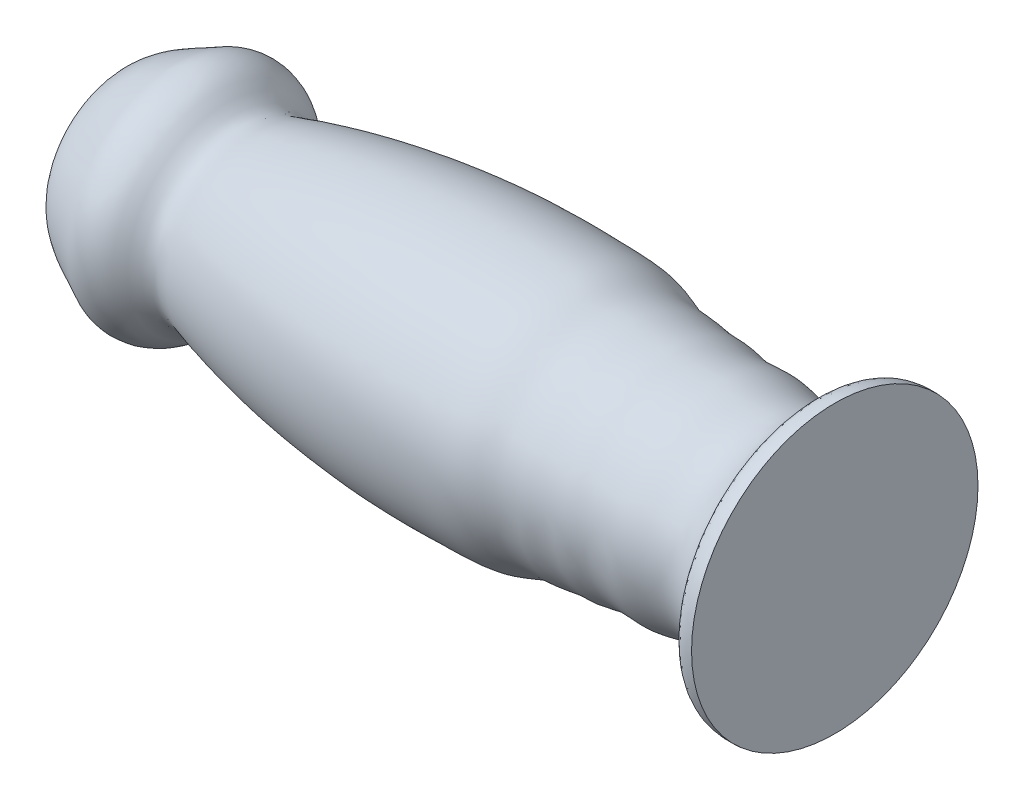
SolidWorks part; units mm, degrees
ref_plane "Front Plane" through (0, 0, 0) normal (0, 0, 1) x (1, 0, 0)
ref_plane "Top Plane" through (0, 0, 0) normal (0, 1, 0) x (1, 0, 0)
ref_plane "Right Plane" through (0, 0, 0) normal (1, 0, 0) x (0, 0, -1)
sketch "Sketch2" plane through (0, 0, 0) normal (0, 1, 0) x (1, 0, 0)
  line L0 (0, 0) -> (76.2, 0) construction
  line L1 (0, -12.7) -> (0, 12.7) construction
  line L2 (41.9716, 155.783) -> (-4.8564, -161.233) construction
  line L3 (-48.8594, 0.7428) -> (21.0217, -260.0572) construction
  line L4 (76.2, 15.2345) -> (76.2, 0)
  line L5 (76.2, 0) -> (0, 0)
  spline S0 degree 3 poles (0, 0) (-0.0143, 1.4775) (0.166, 4.2425) (-0.326, 7.6135) (2.2489, 9.9053) (4.7524, 10.8813) (7.3314, 12.3666) (10.5485, 11.8001) (12.4487, 8.7803) (14.9296, 9.7162) (17.742, 10.4735) (23.0715, 11.7188) (28.7793, 12.5633) (35.419, 13.1824) (40.362, 13.3) (45.5684, 13.1787) (49.2634, 13.0947) (52.1358, 11.6382) (54.6249, 11.7097) (56.5581, 11.2463) (58.6813, 11.3604) (60.9893, 10.6348) (64.4642, 11.339) (69.2158, 9.2572) (73.3406, 12.1818) (74.5072, 15.3021) (75.7201, 15.2434) (76.2, 15.2345) knots 0 0 0 0 0.055251 0.078689 0.114576 0.157673 0.173982 0.214512 0.256404 0.27072 0.29874 0.358374 0.455778 0.496148 0.586001 0.624141 0.674586 0.710131 0.730659 0.758425 0.777505 0.802582 0.839311 0.894938 0.967428 0.981727 1 1 1 1
  point P6 (0, 0)
  dimension "D1" = 76.2
  dimension "D2" = 25.4
revolve "Revolve2" add sketch "Sketch2" angle 360 about L5
equation "\"straightLength\"= 4.0"
equation "\"barThickness\" = .25"
equation "\"angle\" = 30.0"
equation "\"handleDiam\" = 1.0"
equation "\"handleLength\" = 3.0"
